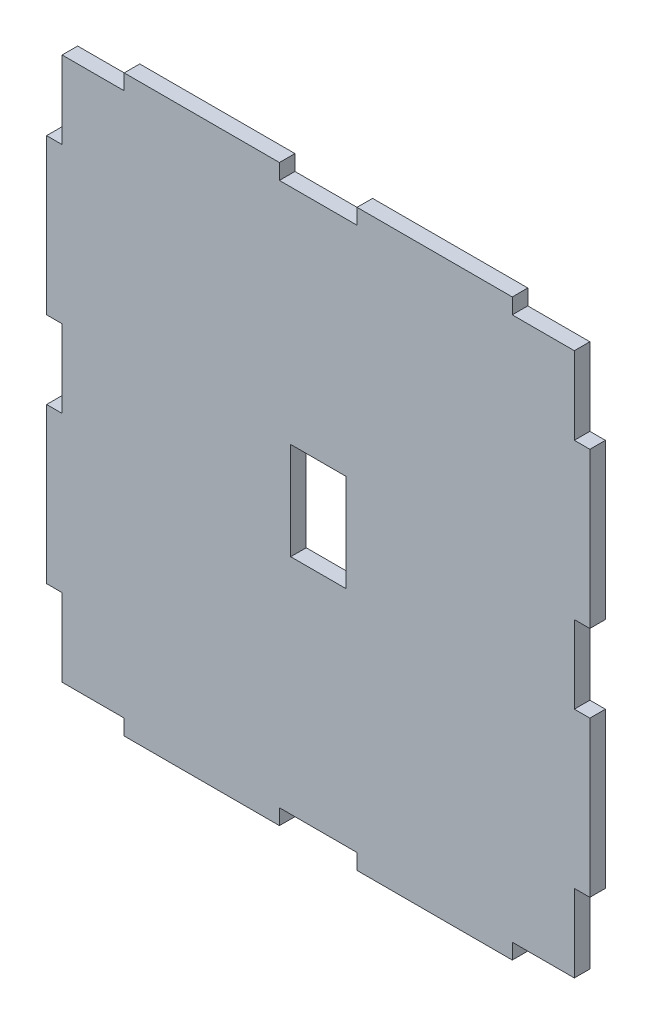
SolidWorks part; units mm, degrees
ref_plane "Front Plane" through (0, 0, 0) normal (0, 0, 1) x (1, 0, 0)
ref_plane "Top Plane" through (0, 0, 0) normal (0, 1, 0) x (1, 0, 0)
ref_plane "Right Plane" through (0, 0, 0) normal (1, 0, 0) x (0, 0, -1)
sketch "Sketch1" plane through (0, 0, 0) normal (0, 0, 1) x (1, 0, 0)
  line L1 (-33, -35) -> (33, -35)
  line L2 (-33, -35) -> (-33, 35)
  line L3 (-33, 35) -> (33, 35)
  line L4 (33, -35) -> (33, 35)
  line L5 (0, 35) -> (0, -35) construction
  line L6 (-33, 0) -> (33, 0) construction
  point P0 (0, 0)
  dimension "D1" = 66
  dimension "D2" = 70
extrude "Boss-Extrude1" add sketch "Sketch1" along normal blind 2
sketch "Sketch2" plane through (0, 0, 0) normal (0, 0, -1) x (-1, 0, 0)
  line L0 (-33, -35) -> (-33, 35) construction
  line L1 (-31, 5) -> (-35, 5)
  line L2 (-31, 5) -> (-31, -5)
  line L3 (-31, -5) -> (-35, -5)
  line L4 (-35, 5) -> (-35, -5)
  line L5 (-33, -5) -> (-33, 5) construction
  line L6 (-31, 0) -> (-35, 0) construction
  line L7 (-33, -35) -> (-33, 0)
  line L8 (-33, -5) -> (-35, -5)
  line L9 (-33, -5) -> (-33, -25)
  line L10 (-33, -25) -> (-35, -25)
  line L11 (-35, -5) -> (-35, -25)
  line L12 (-33, 5) -> (-35, 5)
  line L13 (-33, 5) -> (-33, 25)
  line L14 (-33, 25) -> (-35, 25)
  line L15 (-35, 5) -> (-35, 25)
  line L16 (35, 5) -> (31, 5)
  line L17 (35, 5) -> (35, -5)
  line L18 (35, -5) -> (31, -5)
  line L19 (31, 5) -> (31, -5)
  line L20 (33, -5) -> (33, 5) construction
  line L21 (35, 0) -> (31, 0) construction
  line L22 (33, -35) -> (33, 0)
  line L23 (33, -5) -> (31, -5)
  line L24 (33, -5) -> (33, -25)
  line L25 (33, -25) -> (31, -25)
  line L26 (31, -5) -> (31, -25)
  line L27 (33, 5) -> (31, 5)
  line L28 (33, 5) -> (33, 25)
  line L29 (33, 25) -> (31, 25)
  line L30 (31, 5) -> (31, 25)
  line L32 (33, -5) -> (35, -5)
  line L33 (33, -5) -> (33, -25)
  line L34 (33, -25) -> (35, -25)
  line L35 (35, -5) -> (35, -25)
  line L36 (35, 5) -> (33, 5)
  line L37 (35, 5) -> (35, 25)
  line L38 (35, 25) -> (33, 25)
  line L39 (33, 5) -> (33, 25)
  point P0 (-33, 0)
  point P12 (33, 0)
  line M5 (-33, 35) -> (-33, -35)
  line M7 (33, -35) -> (33, 35)
  dimension "D1" = 4
  dimension "D2" = 10
  dimension "D3" = 20
  dimension "D4" = 20
  dimension "D5" = 4
  dimension "D6" = 10
  dimension "D7" = 20
  dimension "D8" = 20
  dimension "D9" = 35
  dimension "D10" = 35
extrude "Boss-Extrude2" add sketch "Sketch2" against normal blind 2 contours L35 L18 L22 L34 | L37 L38 L16 M7 | L3 L11 L10 M5 | L15 L1 L14 M5
sketch "Sketch3" plane through (0, 0, 0) normal (0, 0, -1) x (-1, 0, 0)
  line L0 (-33, -35) -> (0, -35)
  line L1 (33, -35) -> (-33, -35) construction
  line L2 (-33, 35) -> (0, 35)
  line L3 (-5, -37) -> (5, -37)
  line L4 (-5, -37) -> (-5, -33)
  line L5 (-5, -33) -> (5, -33)
  line L6 (5, -37) -> (5, -33)
  line L7 (0, -33) -> (0, -37) construction
  line L8 (-5, -35) -> (5, -35) construction
  line L9 (5, -35) -> (25, -35)
  line L10 (5, -35) -> (5, -37)
  line L11 (5, -37) -> (25, -37)
  line L12 (25, -35) -> (25, -37)
  line L13 (-5, -35) -> (-25, -35)
  line L14 (-5, -35) -> (-5, -37)
  line L15 (-5, -37) -> (-25, -37)
  line L16 (-25, -35) -> (-25, -37)
  line L17 (-5, 33) -> (5, 33)
  line L18 (-5, 33) -> (-5, 37)
  line L19 (-5, 37) -> (5, 37)
  line L20 (5, 33) -> (5, 37)
  line L21 (0, 37) -> (0, 33) construction
  line L22 (-5, 35) -> (5, 35) construction
  line L23 (5, 35) -> (25, 35)
  line L24 (5, 35) -> (5, 33)
  line L25 (5, 33) -> (25, 33)
  line L26 (25, 35) -> (25, 33)
  line L27 (-5, 35) -> (-25, 35)
  line L28 (-5, 35) -> (-5, 33)
  line L29 (-5, 33) -> (-25, 33)
  line L30 (-25, 35) -> (-25, 33)
  line L32 (-25, 35) -> (-5, 35)
  line L33 (-25, 35) -> (-25, 37)
  line L34 (-25, 37) -> (-5, 37)
  line L35 (-5, 35) -> (-5, 37)
  line L36 (5, 35) -> (25, 35)
  line L37 (5, 35) -> (5, 37)
  line L38 (5, 37) -> (25, 37)
  line L39 (25, 35) -> (25, 37)
  line M6 (-33, -35) -> (33, -35)
  line M16 (33, 35) -> (-33, 35)
  dimension "D1" = 10
  dimension "D2" = 4
  dimension "D3" = 33
  dimension "D4" = 20
  dimension "D5" = 20
  dimension "D6" = 33
  dimension "D7" = 20
  dimension "D8" = 20
extrude "Boss-Extrude3" add sketch "Sketch3" against normal blind 2 contours L34 L33 L2 L18 | L39 L38 L20 M16 | L0 L16 L15 L4 | L12 L6 L11 M6
sketch "Sketch4" plane through (0, 0, 0) normal (0, 0, -1) x (-1, 0, 0)
  line L1 (-3.55, -6.265) -> (3.55, -6.265)
  line L2 (-3.55, -6.265) -> (-3.55, 6.265)
  line L3 (-3.55, 6.265) -> (3.55, 6.265)
  line L4 (3.55, -6.265) -> (3.55, 6.265)
  line L5 (0, 6.265) -> (0, -6.265) construction
  line L6 (-3.55, 0) -> (3.55, 0) construction
  point P0 (0, 0)
  dimension "D1" = 7.1
  dimension "D2" = 12.53
extrude "Cut-Extrude1" cut sketch "Sketch4" against normal blind 10
